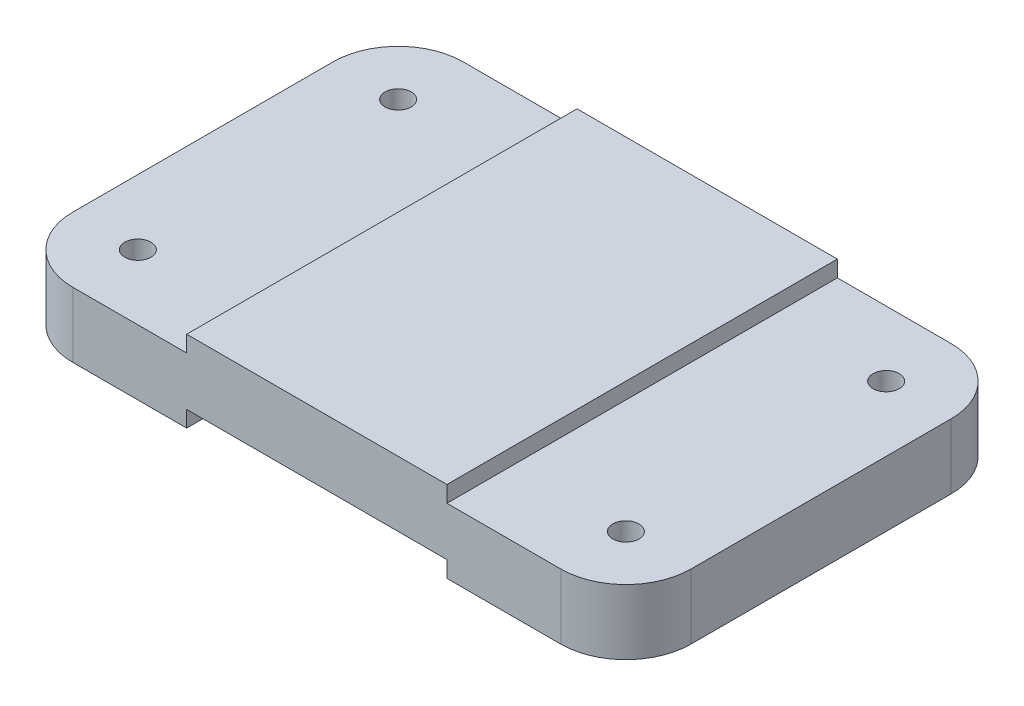
SolidWorks part; units mm, degrees
ref_plane "Front Plane" through (0, 0, 0) normal (0, 0, 1) x (1, 0, 0)
ref_plane "Top Plane" through (0, 0, 0) normal (0, 1, 0) x (1, 0, 0)
ref_plane "Right Plane" through (0, 0, 0) normal (1, 0, 0) x (0, 0, -1)
sketch "Sketch1" plane through (0, 0, 0) normal (0, 0, 1) x (1, 0, 0)
  line L0 (-3.3867, 0) -> (31.5383, 0)
  line L1 (31.5383, 0) -> (31.5383, 3.175)
  line L2 (31.5383, 3.175) -> (82.3383, 3.175)
  line L3 (82.3383, 3.175) -> (82.3383, 0)
  line L4 (82.3383, 0) -> (117.2633, 0)
  line L5 (117.2633, 0) -> (117.2633, 12.7)
  line L6 (117.2633, 12.7) -> (82.3383, 12.7)
  line L7 (82.3383, 12.7) -> (82.3383, 15.875)
  line L8 (82.3383, 15.875) -> (31.5383, 15.875)
  line L9 (31.5383, 15.875) -> (31.5383, 12.7)
  line L10 (31.5383, 12.7) -> (-3.3867, 12.7)
  line L11 (-3.3867, 12.7) -> (-3.3867, 0)
  line L12 (-3.3867, 25.4) -> (-3.3867, 12.7) construction
  point P3 (31.5383, 1.5875)
  dimension "D1" = 15.875
  dimension "D2" = 120.65
  dimension "D3" = 3.175
  dimension "D4" = 50.8
  dimension "D5" = 34.925
extrude "Boss-Extrude1" add sketch "Sketch1" against normal blind 76.2
fillet "Fillet1" radius 12.7 4 edges at (117.2633, 6.35, -76.2) (-3.3867, 6.35, -76.2) (-3.3867, 6.35, 0) (117.2633, 6.35, 0)
hole_wizard "1/4-20 Tapped Hole3" positions "Sketch19" profile "Sketch20" tap size "1/4-20" standard "ANSI Inch"
sketch "Sketch19" plane through (0, 12.7, 0) normal (0, 1, 0) x (1, 0, 0)
  point P0 (104.5633, 63.5)
  point P3 (104.5633, 12.7)
  point P6 (9.3133, 12.7)
  point P9 (9.3133, 63.5)
sketch "Sketch20" plane through (104.5633, 12.7, -63.5) normal (1, 0, 0) x (0, 0, 1)
  line L0 (0, 0) -> (0, 18.0438)
  line L1 (0, 18.0438) -> (2.5527, 16.51)
  line L2 (2.5527, 16.51) -> (2.5527, 0)
  line L5 (2.5527, 0) -> (0, 0)
  line L10 (0, 18.0438) -> (-2.5527, 16.51) construction
  line L11 (0, -6.35) -> (0, 107.95) construction
  dimension "Tap Drill Dia." = 5.1054
  dimension "Tap Drill Depth" = 16.51
  dimension "Drill Angle" = 118
cosmetic thread "Hole Thread3" parameters "D1"=12.7, "D2"=6.35
cosmetic thread "Hole Thread4" parameters "D1"=12.7, "D2"=6.35
cosmetic thread "Hole Thread5" parameters "D1"=12.7, "D2"=6.35
cosmetic thread "Hole Thread6" parameters "D1"=12.7, "D2"=6.35
